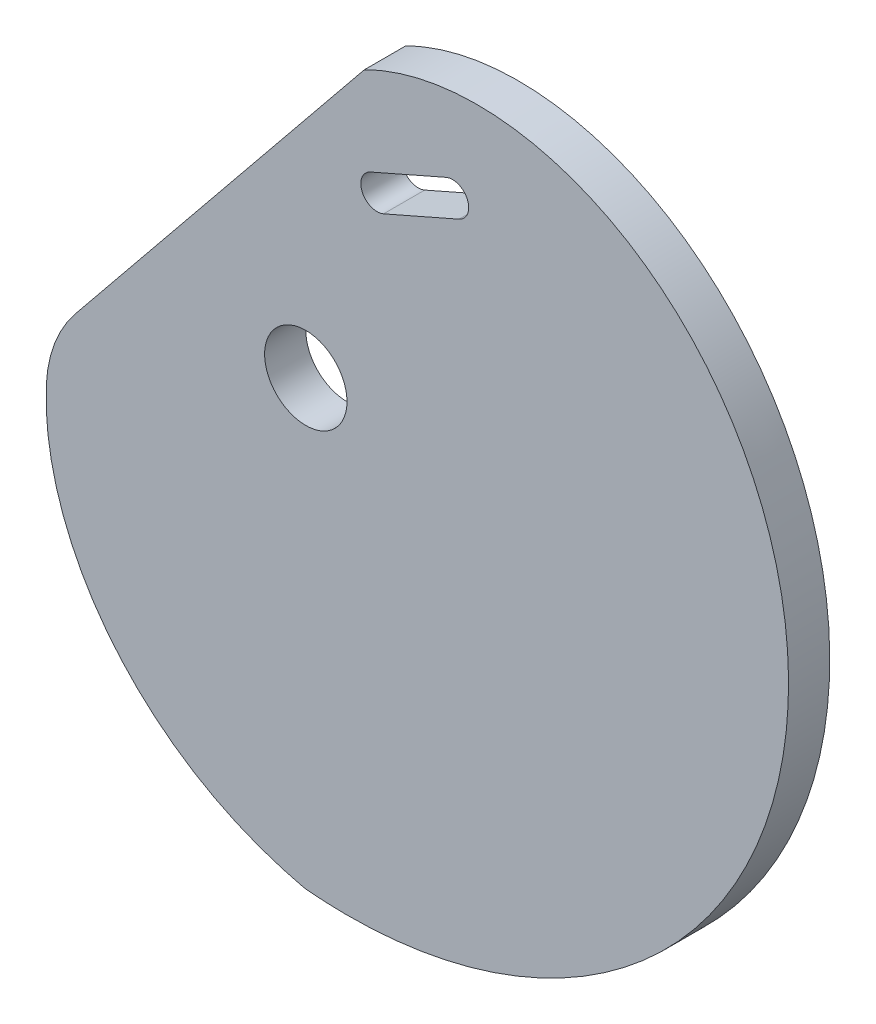
SolidWorks part; units mm, degrees
ref_plane "Front Plane" through (0, 0, 0) normal (0, 0, 1) x (1, 0, 0)
ref_plane "Top Plane" through (0, 0, 0) normal (0, 1, 0) x (1, 0, 0)
ref_plane "Right Plane" through (0, 0, 0) normal (1, 0, 0) x (0, 0, -1)
curve "Curve1"
sketch "Sketch1" plane through (0, 0, 0) normal (0, 0, 1) x (1, 0, 0)
  line L0 (10.9805, 30.1851) -> (22.6104, 35.2876) construction
  line L1 (9.976, 32.4744) -> (21.6059, 37.5769)
  line L2 (11.9849, 27.8957) -> (23.6148, 32.9983)
  line L3 (10.7688, 46.4724) -> (16.7954, 32.7363) construction
  line L4 (-15.5247, -36.542) -> (-17.0714, -47.8252) construction
  line L5 (-12.072, -37.0153) -> (-13.6188, -48.2986) construction
  line L6 (-18.9773, -36.0687) -> (-20.5241, -47.3519) construction
  line L7 (-15.1851, -34.0651) -> (-15.8642, -39.0188) construction
  circle A0 centre (0, 0) radius 6.35
  arc A1 (9.976, 32.4744) -> (11.9849, 27.8957) centre (10.9805, 30.1851) ccw
  arc A2 (23.6148, 32.9983) -> (21.6059, 37.5769) centre (22.6104, 35.2876) ccw
  arc A4 (-12.072, -37.0153) -> (-18.9773, -36.0687) centre (-15.5247, -36.542) ccw construction
  arc A5 (-20.5241, -47.3519) -> (-13.6188, -48.2986) centre (-17.0714, -47.8252) ccw construction
  spline S1 degree 3 poles (-1.1843, -67.9504) (-0.014, -68.2767) (1.195, -68.3213) (2.3889, -68.4148) (3.5889, -68.4701) (4.791, -68.5105) (5.9959, -68.5295) (7.203, -68.5287) (8.412, -68.5074) (9.6226, -68.4657) (10.8344, -68.4032) (12.047, -68.32) (13.2602, -68.2159) (14.4735, -68.0908) (15.6866, -67.9446) (16.8991, -67.777) (18.1106, -67.5882) (19.3207, -67.3779) (20.529, -67.1461) (21.7351, -66.8927) (22.9386, -66.6176) (24.1392, -66.3208) (25.3362, -66.0022) (26.5295, -65.6619) (27.7184, -65.2996) (28.9026, -64.9155) (30.0816, -64.5096) (31.2551, -64.0817) (32.4225, -63.632) (33.5833, -63.1604) (34.7372, -62.667) (35.8837, -62.1518) (37.0223, -61.6149) (38.1525, -61.0563) (39.2739, -60.4761) (40.3861, -59.8743) (41.4885, -59.2512) (42.5806, -58.6068) (43.6621, -57.9411) (44.7324, -57.2544) (45.791, -56.5468) (46.8375, -55.8184) (47.8714, -55.0695) (48.8923, -54.3001) (49.8996, -53.5105) (50.8929, -52.7009) (51.8717, -51.8715) (52.8356, -51.0225) (53.7841, -50.1542) (54.7166, -49.2668) (55.6329, -48.3607) (56.5323, -47.436) (57.4145, -46.4932) (58.279, -45.5324) (59.1254, -44.554) (59.9531, -43.5583) (60.7619, -42.5458) (61.5512, -41.5167) (62.3207, -40.4714) (63.0698, -39.4103) (63.7983, -38.3338) (64.5057, -37.2423) (65.1916, -36.1362) (65.8556, -35.016) (66.4973, -33.882) (67.1165, -32.7348) (67.7126, -31.5748) (68.2854, -30.4026) (68.8345, -29.2185) (69.3596, -28.023) (69.8603, -26.8168) (70.3364, -25.6003) (70.7876, -24.3741) (71.2134, -23.1386) (71.6138, -21.8945) (71.9884, -20.6423) (72.337, -19.3826) (72.6592, -18.116) (72.955, -16.843) (73.224, -15.5643) (73.4661, -14.2804) (73.6812, -12.992) (73.8689, -11.6997) (74.0292, -10.4042) (74.1619, -9.106) (74.2669, -7.8058) (74.3441, -6.5043) (74.3933, -5.2021) (74.4146, -3.9) (74.4078, -2.5984) (74.3729, -1.2982) (74.3098, -0.0001) (74.2186, 1.2954) (74.0993, 2.5875) (73.9518, 3.8756) (73.7762, 5.1589) (73.5725, 6.4367) (73.3409, 7.7084) (73.0814, 8.9732) (72.7942, 10.2305) (72.4792, 11.4795) (72.1368, 12.7196) (71.767, 13.95) (71.3701, 15.1701) (70.9462, 16.3792) (70.4955, 17.5765) (70.0184, 18.7613) (69.515, 19.9331) (68.9856, 21.091) (68.4305, 22.2344) (67.85, 23.3626) (67.2445, 24.475) (66.6143, 25.5709) (65.9598, 26.6495) (65.2813, 27.7103) (64.5793, 28.7526) (63.8542, 29.7758) (63.1064, 30.7792) (62.3364, 31.7621) (61.5447, 32.7241) (60.7318, 33.6643) (59.8981, 34.5824) (59.0442, 35.4776) (58.1707, 36.3494) (57.2782, 37.1972) (56.3671, 38.0204) (55.4383, 38.8186) (54.4923, 39.5913) (53.53, 40.3381) (52.552, 41.0585) (51.5591, 41.7521) (50.552, 42.4186) (49.5315, 43.0576) (48.4984, 43.6687) (47.4535, 44.2516) (46.3974, 44.8061) (45.3311, 45.3318) (44.2553, 45.8284) (43.1709, 46.2958) (42.0786, 46.7338) (40.9793, 47.1421) (39.8737, 47.5205) (38.7628, 47.869) (37.6473, 48.1874) (36.5281, 48.4755) (35.4061, 48.7334) (34.282, 48.961) (33.1567, 49.1581) (32.031, 49.3249) (30.9059, 49.4613) (29.7821, 49.5673) (28.6604, 49.6431) (27.5418, 49.6886) (26.427, 49.7041) (25.3169, 49.6895) (24.2124, 49.6451) (23.1141, 49.571) (22.0231, 49.4674) (20.94, 49.3346) (19.8657, 49.1727) (18.801, 48.982) (17.7468, 48.7628) (16.7037, 48.5154) (15.6726, 48.2401) (14.6543, 47.9373) (13.6495, 47.6073) (12.659, 47.2504) (11.6836, 46.8672) (10.7239, 46.458) (9.7807, 46.0233) (8.8547, 45.5635) (7.9467, 45.0791) (7.0573, 44.5706) (6.1871, 44.0386) (5.3369, 43.4835) (4.5074, 42.906) (3.699, 42.3065) (2.9126, 41.6858) (2.1491, 41.0448) (1.4087, 40.3857) (0.692, 39.711) (-0.0007, 39.0233) (-0.6692, 38.3252) (-1.3135, 37.6192) (-1.9336, 36.908) (-2.5298, 36.194) (-3.1024, 35.4799) (-3.6521, 34.7682) (-4.1795, 34.0612) (-4.6854, 33.3616) (-5.1709, 32.6716) (-5.637, 31.9937) (-6.085, 31.3301) (-6.5163, 30.6831) (-6.9325, 30.0548) (-7.3352, 29.4474) (-7.7263, 28.8629) (-8.1078, 28.3032) (-8.4816, 27.77) (-8.8501, 27.2652) (-9.216, 26.7897) (-9.5801, 26.3424) (-9.9432, 25.9213) (-10.3062, 25.5243) (-10.6698, 25.1494) (-11.0346, 24.7946) (-11.4009, 24.4578) (-11.7691, 24.1369) (-12.1394, 23.8299) (-12.5117, 23.5348) (-12.8861, 23.2497) (-13.2622, 22.9725) (-13.6397, 22.7014) (-14.0182, 22.4345) (-14.3971, 22.1699) (-14.7757, 21.906) (-15.1531, 21.6409) (-15.5285, 21.3732) (-15.9009, 21.1012) (-16.269, 20.8234) (-16.6317, 20.5384) (-16.9875, 20.2449) (-17.3351, 19.9417) (-17.6745, 19.6295) (-18.0059, 19.3089) (-18.3295, 18.9807) (-18.6455, 18.6455) (-18.9542, 18.3039) (-19.2559, 17.9565) (-19.5509, 17.6038) (-19.8396, 17.2464) (-20.1224, 16.8848) (-20.3997, 16.5195) (-20.672, 16.1508) (-20.9397, 15.7793) (-21.2033, 15.4052) (-21.4634, 15.0289) (-21.7205, 14.6507) (-21.9753, 14.2708) (-22.2281, 13.8895) (-22.4798, 13.507) (-22.7308, 13.1233) (-22.9819, 12.7386) (-23.2336, 12.3529) (-23.4866, 11.9663) (-23.7416, 11.5787) (-23.9993, 11.19) (-24.2602, 10.8001) (-24.5251, 10.4088) (-24.7947, 10.016) (-25.0696, 9.6214) (-25.3504, 9.2246) (-25.6379, 8.8254) (-25.9327, 8.4234) (-26.2354, 8.018) (-26.5467, 7.609) (-26.8672, 7.1956) (-27.1974, 6.7776) (-27.537, 6.3539) (-27.8856, 5.9238) (-28.2424, 5.4864) (-28.6069, 5.0408) (-28.9783, 4.5865) (-29.3562, 4.1226) (-29.7396, 3.6485) (-30.1278, 3.1637) (-30.5202, 2.6674) (-30.9158, 2.1592) (-31.314, 1.6386) (-31.7137, 1.1051) (-32.1143, 0.5583) (-32.5148, -0.0021) (-32.9143, -0.5765) (-33.3119, -1.1651) (-33.7067, -1.7682) (-34.0978, -2.3859) (-34.4843, -3.0184) (-34.8652, -3.6658) (-35.2396, -4.3281) (-35.6066, -5.0053) (-35.9651, -5.6973) (-36.3143, -6.404) (-36.6531, -7.1254) (-36.9808, -7.8611) (-37.2963, -8.611) (-37.5988, -9.3748) (-37.8873, -10.1521) (-38.1609, -10.9426) (-38.4187, -11.7459) (-38.66, -12.5613) (-38.8837, -13.3886) (-39.0892, -14.2271) (-39.2755, -15.0762) (-39.4422, -15.9354) (-39.589, -16.8043) (-39.7155, -17.6823) (-39.8215, -18.5689) (-39.9067, -19.4636) (-39.9709, -20.366) (-40.0137, -21.2755) (-40.035, -22.1916) (-40.0345, -23.1138) (-40.0119, -24.0415) (-39.9672, -24.9742) (-39.9002, -25.9114) (-39.8105, -26.8525) (-39.6982, -27.7969) (-39.563, -28.7442) (-39.4048, -29.6936) (-39.2235, -30.6448) (-39.019, -31.597) (-38.7911, -32.5497) (-38.5399, -33.5023) (-38.2653, -34.4543) (-37.9672, -35.4051) (-37.6456, -36.354) (-37.3004, -37.3005) (-36.9317, -38.2441) (-36.5395, -39.184) (-36.1238, -40.1197) (-35.6847, -41.0507) (-35.2221, -41.9763) (-34.7363, -42.896) (-34.2272, -43.8091) (-33.695, -44.715) (-33.1398, -45.6133) (-32.5617, -46.5032) (-31.9609, -47.3843) (-31.3375, -48.2559) (-30.6917, -49.1174) (-30.0238, -49.9683) (-29.3338, -50.808) (-28.6221, -51.636) (-27.8888, -52.4517) (-27.1343, -53.2545) (-26.3587, -54.0439) (-25.5624, -54.8193) (-24.7457, -55.5802) (-23.9088, -56.3261) (-23.0521, -57.0564) (-22.1759, -57.7707) (-21.2805, -58.4684) (-20.3664, -59.149) (-19.4339, -59.812) (-18.4833, -60.4569) (-17.5151, -61.0833) (-16.5298, -61.6908) (-15.5276, -62.2787) (-14.5091, -62.8467) (-13.4747, -63.3944) (-12.4248, -63.9213) (-11.36, -64.4271) (-10.2807, -64.9112) (-9.1874, -65.3733) (-8.0806, -65.8131) (-6.9608, -66.2301) (-5.8286, -66.6239) (-4.6845, -66.9947) (-3.5289, -67.3403) (-2.3631, -67.6669) (-1.1843, -67.9504) (-0.014, -68.2767) (1.195, -68.3213) knots -0.0101 -0.006743 -0.003377 0 0.00332 0.006645 0.009976 0.013312 0.016655 0.020003 0.023357 0.026716 0.030082 0.033453 0.036831 0.040214 0.043603 0.046998 0.050399 0.053806 0.057218 0.060637 0.064061 0.067491 0.070927 0.074369 0.077816 0.081269 0.084728 0.088192 0.091662 0.095138 0.098619 0.102105 0.105597 0.109094 0.112596 0.116103 0.119615 0.123133 0.126655 0.130182 0.133714 0.137251 0.140792 0.144337 0.147888 0.151442 0.155 0.158563 0.16213 0.1657 0.169275 0.172853 0.176434 0.180019 0.183607 0.187199 0.190793 0.19439 0.19799 0.201593 0.205199 0.208806 0.212416 0.216028 0.219642 0.223258 0.226875 0.230494 0.234115 0.237736 0.241359 0.244982 0.248606 0.252231 0.255856 0.259481 0.263106 0.266731 0.270356 0.273981 0.277605 0.281228 0.28485 0.28847 0.29209 0.295708 0.299324 0.302939 0.306551 0.310161 0.313769 0.317374 0.320976 0.324575 0.328171 0.331763 0.335352 0.338938 0.342519 0.346096 0.349669 0.353237 0.356801 0.360359 0.363913 0.367461 0.371004 0.374541 0.378073 0.381598 0.385117 0.38863 0.392136 0.395636 0.399128 0.402614 0.406092 0.409563 0.413026 0.416482 0.419929 0.423369 0.4268 0.430223 0.433637 0.437043 0.44044 0.443828 0.447206 0.450575 0.453935 0.457284 0.460624 0.463953 0.467272 0.47058 0.473877 0.477164 0.480439 0.483703 0.486955 0.490196 0.493426 0.496643 0.499848 0.503042 0.506223 0.509391 0.512547 0.515691 0.518822 0.52194 0.525045 0.528137 0.531216 0.534282 0.537335 0.540375 0.543401 0.546414 0.549414 0.5524 0.555374 0.558333 0.56128 0.564213 0.567133 0.57004 0.572933 0.575814 0.578681 0.581535 0.584377 0.587205 0.590021 0.592825 0.595616 0.598394 0.60116 0.603911 0.606642 0.60935 0.612032 0.614684 0.617303 0.619884 0.622424 0.62492 0.627367 0.629763 0.632104 0.634387 0.636609 0.638767 0.640858 0.64288 0.644831 0.64671 0.648517 0.65025 0.651911 0.653509 0.655048 0.656538 0.657984 0.659394 0.660772 0.662125 0.663458 0.664774 0.666078 0.667373 0.668662 0.669946 0.671227 0.672507 0.673786 0.675065 0.676344 0.677623 0.678903 0.680182 0.681461 0.68274 0.684019 0.685298 0.686575 0.687853 0.689129 0.690404 0.691679 0.692952 0.694224 0.695495 0.696765 0.698035 0.699304 0.700572 0.70184 0.703109 0.704379 0.705651 0.706925 0.708202 0.709483 0.71077 0.712063 0.713364 0.714674 0.715995 0.717328 0.718676 0.72004 0.721422 0.722825 0.72425 0.7257 0.727177 0.728683 0.730218 0.731784 0.73338 0.735008 0.736668 0.738359 0.740082 0.741837 0.743623 0.745441 0.747291 0.749171 0.751082 0.753022 0.754993 0.756992 0.759021 0.761077 0.76316 0.765271 0.767407 0.769569 0.771756 0.773967 0.776201 0.778458 0.780736 0.783036 0.785357 0.787697 0.790056 0.792433 0.794828 0.797239 0.799666 0.80211 0.804571 0.807047 0.80954 0.812049 0.814575 0.817116 0.819674 0.822248 0.824838 0.827444 0.830066 0.832704 0.835358 0.838027 0.840713 0.843414 0.846131 0.848864 0.851612 0.854376 0.857155 0.859949 0.862759 0.865584 0.868424 0.871279 0.874149 0.877033 0.879933 0.882847 0.885776 0.88872 0.891678 0.89465 0.897636 0.900637 0.903651 0.906679 0.909721 0.912777 0.915847 0.91893 0.922026 0.925135 0.928258 0.931393 0.934541 0.937702 0.940876 0.944062 0.947261 0.950471 0.953694 0.956929 0.960175 0.963433 0.966703 0.969984 0.973276 0.976579 0.979893 0.983218 0.986554 0.9899 0.993257 0.996623 1 1.00332 1.006645 1.009976 only from (0, -68.2309) to (0, -68.2309)
  point P6 (16.7954, 32.7363)
  point P18 (-16.298, -42.1836)
  dimension "D1" = 12.7
  dimension "D2" = 12.7
  dimension "D3" = 5
  dimension "D4" = 15
extrude "Boss-Extrude1" add sketch "Sketch1" along normal mid plane 6.35
sketch "Sketch2" plane through (0, 0, 0) normal (0, 0, 1) x (1, 0, 0)
  line L0 (7.479, 46.6391) -> (-35.7001, -3.6508) construction
  line L1 (-35.7001, -3.6508) -> (-5.287, 46.6391)
  line L2 (-5.287, 46.6391) -> (7.479, 46.6391)
  line L3 (9.0178, 45.6413) -> (-41.2002, -16.1969)
  line L4 (7.479, 46.6391) -> (9.0178, 45.6413)
  line L5 (-35.7001, -3.6508) -> (-41.2002, -16.1969)
  spline S0 degree 3 poles (-1.1843, -67.9504) (-0.014, -68.2767) (1.195, -68.3213) (2.3889, -68.4148) (3.5889, -68.4701) (4.791, -68.5105) (5.9959, -68.5295) (7.203, -68.5287) (8.412, -68.5074) (9.6226, -68.4657) (10.8344, -68.4032) (12.047, -68.32) (13.2602, -68.2159) (14.4735, -68.0908) (15.6866, -67.9446) (16.8991, -67.777) (18.1106, -67.5882) (19.3207, -67.3779) (20.529, -67.1461) (21.7351, -66.8927) (22.9386, -66.6176) (24.1392, -66.3208) (25.3362, -66.0022) (26.5295, -65.6619) (27.7184, -65.2996) (28.9026, -64.9155) (30.0816, -64.5096) (31.2551, -64.0817) (32.4225, -63.632) (33.5833, -63.1604) (34.7372, -62.667) (35.8837, -62.1518) (37.0223, -61.6149) (38.1525, -61.0563) (39.2739, -60.4761) (40.3861, -59.8743) (41.4885, -59.2512) (42.5806, -58.6068) (43.6621, -57.9411) (44.7324, -57.2544) (45.791, -56.5468) (46.8375, -55.8184) (47.8714, -55.0695) (48.8923, -54.3001) (49.8996, -53.5105) (50.8929, -52.7009) (51.8717, -51.8715) (52.8356, -51.0225) (53.7841, -50.1542) (54.7166, -49.2668) (55.6329, -48.3607) (56.5323, -47.436) (57.4145, -46.4932) (58.279, -45.5324) (59.1254, -44.554) (59.9531, -43.5583) (60.7619, -42.5458) (61.5512, -41.5167) (62.3207, -40.4714) (63.0698, -39.4103) (63.7983, -38.3338) (64.5057, -37.2423) (65.1916, -36.1362) (65.8556, -35.016) (66.4973, -33.882) (67.1165, -32.7348) (67.7126, -31.5748) (68.2854, -30.4026) (68.8345, -29.2185) (69.3596, -28.023) (69.8603, -26.8168) (70.3364, -25.6003) (70.7876, -24.3741) (71.2134, -23.1386) (71.6138, -21.8945) (71.9884, -20.6423) (72.337, -19.3826) (72.6592, -18.116) (72.955, -16.843) (73.224, -15.5643) (73.4661, -14.2804) (73.6812, -12.992) (73.8689, -11.6997) (74.0292, -10.4042) (74.1619, -9.106) (74.2669, -7.8058) (74.3441, -6.5043) (74.3933, -5.2021) (74.4146, -3.9) (74.4078, -2.5984) (74.3729, -1.2982) (74.3098, -0.0001) (74.2186, 1.2954) (74.0993, 2.5875) (73.9518, 3.8756) (73.7762, 5.1589) (73.5725, 6.4367) (73.3409, 7.7084) (73.0814, 8.9732) (72.7942, 10.2305) (72.4792, 11.4795) (72.1368, 12.7196) (71.767, 13.95) (71.3701, 15.1701) (70.9462, 16.3792) (70.4955, 17.5765) (70.0184, 18.7613) (69.515, 19.9331) (68.9856, 21.091) (68.4305, 22.2344) (67.85, 23.3626) (67.2445, 24.475) (66.6143, 25.5709) (65.9598, 26.6495) (65.2813, 27.7103) (64.5793, 28.7526) (63.8542, 29.7758) (63.1064, 30.7792) (62.3364, 31.7621) (61.5447, 32.7241) (60.7318, 33.6643) (59.8981, 34.5824) (59.0442, 35.4776) (58.1707, 36.3494) (57.2782, 37.1972) (56.3671, 38.0204) (55.4383, 38.8186) (54.4923, 39.5913) (53.53, 40.3381) (52.552, 41.0585) (51.5591, 41.7521) (50.552, 42.4186) (49.5315, 43.0576) (48.4984, 43.6687) (47.4535, 44.2516) (46.3974, 44.8061) (45.3311, 45.3318) (44.2553, 45.8284) (43.1709, 46.2958) (42.0786, 46.7338) (40.9793, 47.1421) (39.8737, 47.5205) (38.7628, 47.869) (37.6473, 48.1874) (36.5281, 48.4755) (35.4061, 48.7334) (34.282, 48.961) (33.1567, 49.1581) (32.031, 49.3249) (30.9059, 49.4613) (29.7821, 49.5673) (28.6604, 49.6431) (27.5418, 49.6886) (26.427, 49.7041) (25.3169, 49.6895) (24.2124, 49.6451) (23.1141, 49.571) (22.0231, 49.4674) (20.94, 49.3346) (19.8657, 49.1727) (18.801, 48.982) (17.7468, 48.7628) (16.7037, 48.5154) (15.6726, 48.2401) (14.6543, 47.9373) (13.6495, 47.6073) (12.659, 47.2504) (11.6836, 46.8672) (10.7239, 46.458) (9.7807, 46.0233) (8.8547, 45.5635) (7.9467, 45.0791) (7.0573, 44.5706) (6.1871, 44.0386) (5.3369, 43.4835) (4.5074, 42.906) (3.699, 42.3065) (2.9126, 41.6858) (2.1491, 41.0448) (1.4087, 40.3857) (0.692, 39.711) (-0.0007, 39.0233) (-0.6692, 38.3252) (-1.3135, 37.6192) (-1.9336, 36.908) (-2.5298, 36.194) (-3.1024, 35.4799) (-3.6521, 34.7682) (-4.1795, 34.0612) (-4.6854, 33.3616) (-5.1709, 32.6716) (-5.637, 31.9937) (-6.085, 31.3301) (-6.5163, 30.6831) (-6.9325, 30.0548) (-7.3352, 29.4474) (-7.7263, 28.8629) (-8.1078, 28.3032) (-8.4816, 27.77) (-8.8501, 27.2652) (-9.216, 26.7897) (-9.5801, 26.3424) (-9.9432, 25.9213) (-10.3062, 25.5243) (-10.6698, 25.1494) (-11.0346, 24.7946) (-11.4009, 24.4578) (-11.7691, 24.1369) (-12.1394, 23.8299) (-12.5117, 23.5348) (-12.8861, 23.2497) (-13.2622, 22.9725) (-13.6397, 22.7014) (-14.0182, 22.4345) (-14.3971, 22.1699) (-14.7757, 21.906) (-15.1531, 21.6409) (-15.5285, 21.3732) (-15.9009, 21.1012) (-16.269, 20.8234) (-16.6317, 20.5384) (-16.9875, 20.2449) (-17.3351, 19.9417) (-17.6745, 19.6295) (-18.0059, 19.3089) (-18.3295, 18.9807) (-18.6455, 18.6455) (-18.9542, 18.3039) (-19.2559, 17.9565) (-19.5509, 17.6038) (-19.8396, 17.2464) (-20.1224, 16.8848) (-20.3997, 16.5195) (-20.672, 16.1508) (-20.9397, 15.7793) (-21.2033, 15.4052) (-21.4634, 15.0289) (-21.7205, 14.6507) (-21.9753, 14.2708) (-22.2281, 13.8895) (-22.4798, 13.507) (-22.7308, 13.1233) (-22.9819, 12.7386) (-23.2336, 12.3529) (-23.4866, 11.9663) (-23.7416, 11.5787) (-23.9993, 11.19) (-24.2602, 10.8001) (-24.5251, 10.4088) (-24.7947, 10.016) (-25.0696, 9.6214) (-25.3504, 9.2246) (-25.6379, 8.8254) (-25.9327, 8.4234) (-26.2354, 8.018) (-26.5467, 7.609) (-26.8672, 7.1956) (-27.1974, 6.7776) (-27.537, 6.3539) (-27.8856, 5.9238) (-28.2424, 5.4864) (-28.6069, 5.0408) (-28.9783, 4.5865) (-29.3562, 4.1226) (-29.7396, 3.6485) (-30.1278, 3.1637) (-30.5202, 2.6674) (-30.9158, 2.1592) (-31.314, 1.6386) (-31.7137, 1.1051) (-32.1143, 0.5583) (-32.5148, -0.0021) (-32.9143, -0.5765) (-33.3119, -1.1651) (-33.7067, -1.7682) (-34.0978, -2.3859) (-34.4843, -3.0184) (-34.8652, -3.6658) (-35.2396, -4.3281) (-35.6066, -5.0053) (-35.9651, -5.6973) (-36.3143, -6.404) (-36.6531, -7.1254) (-36.9808, -7.8611) (-37.2963, -8.611) (-37.5988, -9.3748) (-37.8873, -10.1521) (-38.1609, -10.9426) (-38.4187, -11.7459) (-38.66, -12.5613) (-38.8837, -13.3886) (-39.0892, -14.2271) (-39.2755, -15.0762) (-39.4422, -15.9354) (-39.589, -16.8043) (-39.7155, -17.6823) (-39.8215, -18.5689) (-39.9067, -19.4636) (-39.9709, -20.366) (-40.0137, -21.2755) (-40.035, -22.1916) (-40.0345, -23.1138) (-40.0119, -24.0415) (-39.9672, -24.9742) (-39.9002, -25.9114) (-39.8105, -26.8525) (-39.6982, -27.7969) (-39.563, -28.7442) (-39.4048, -29.6936) (-39.2235, -30.6448) (-39.019, -31.597) (-38.7911, -32.5497) (-38.5399, -33.5023) (-38.2653, -34.4543) (-37.9672, -35.4051) (-37.6456, -36.354) (-37.3004, -37.3005) (-36.9317, -38.2441) (-36.5395, -39.184) (-36.1238, -40.1197) (-35.6847, -41.0507) (-35.2221, -41.9763) (-34.7363, -42.896) (-34.2272, -43.8091) (-33.695, -44.715) (-33.1398, -45.6133) (-32.5617, -46.5032) (-31.9609, -47.3843) (-31.3375, -48.2559) (-30.6917, -49.1174) (-30.0238, -49.9683) (-29.3338, -50.808) (-28.6221, -51.636) (-27.8888, -52.4517) (-27.1343, -53.2545) (-26.3587, -54.0439) (-25.5624, -54.8193) (-24.7457, -55.5802) (-23.9088, -56.3261) (-23.0521, -57.0564) (-22.1759, -57.7707) (-21.2805, -58.4684) (-20.3664, -59.149) (-19.4339, -59.812) (-18.4833, -60.4569) (-17.5151, -61.0833) (-16.5298, -61.6908) (-15.5276, -62.2787) (-14.5091, -62.8467) (-13.4747, -63.3944) (-12.4248, -63.9213) (-11.36, -64.4271) (-10.2807, -64.9112) (-9.1874, -65.3733) (-8.0806, -65.8131) (-6.9608, -66.2301) (-5.8286, -66.6239) (-4.6845, -66.9947) (-3.5289, -67.3403) (-2.3631, -67.6669) (-1.1843, -67.9504) (-0.014, -68.2767) (1.195, -68.3213) knots -0.0101 -0.006743 -0.003377 0 0.00332 0.006645 0.009976 0.013312 0.016655 0.020003 0.023357 0.026716 0.030082 0.033453 0.036831 0.040214 0.043603 0.046998 0.050399 0.053806 0.057218 0.060637 0.064061 0.067491 0.070927 0.074369 0.077816 0.081269 0.084728 0.088192 0.091662 0.095138 0.098619 0.102105 0.105597 0.109094 0.112596 0.116103 0.119615 0.123133 0.126655 0.130182 0.133714 0.137251 0.140792 0.144337 0.147888 0.151442 0.155 0.158563 0.16213 0.1657 0.169275 0.172853 0.176434 0.180019 0.183607 0.187199 0.190793 0.19439 0.19799 0.201593 0.205199 0.208806 0.212416 0.216028 0.219642 0.223258 0.226875 0.230494 0.234115 0.237736 0.241359 0.244982 0.248606 0.252231 0.255856 0.259481 0.263106 0.266731 0.270356 0.273981 0.277605 0.281228 0.28485 0.28847 0.29209 0.295708 0.299324 0.302939 0.306551 0.310161 0.313769 0.317374 0.320976 0.324575 0.328171 0.331763 0.335352 0.338938 0.342519 0.346096 0.349669 0.353237 0.356801 0.360359 0.363913 0.367461 0.371004 0.374541 0.378073 0.381598 0.385117 0.38863 0.392136 0.395636 0.399128 0.402614 0.406092 0.409563 0.413026 0.416482 0.419929 0.423369 0.4268 0.430223 0.433637 0.437043 0.44044 0.443828 0.447206 0.450575 0.453935 0.457284 0.460624 0.463953 0.467272 0.47058 0.473877 0.477164 0.480439 0.483703 0.486955 0.490196 0.493426 0.496643 0.499848 0.503042 0.506223 0.509391 0.512547 0.515691 0.518822 0.52194 0.525045 0.528137 0.531216 0.534282 0.537335 0.540375 0.543401 0.546414 0.549414 0.5524 0.555374 0.558333 0.56128 0.564213 0.567133 0.57004 0.572933 0.575814 0.578681 0.581535 0.584377 0.587205 0.590021 0.592825 0.595616 0.598394 0.60116 0.603911 0.606642 0.60935 0.612032 0.614684 0.617303 0.619884 0.622424 0.62492 0.627367 0.629763 0.632104 0.634387 0.636609 0.638767 0.640858 0.64288 0.644831 0.64671 0.648517 0.65025 0.651911 0.653509 0.655048 0.656538 0.657984 0.659394 0.660772 0.662125 0.663458 0.664774 0.666078 0.667373 0.668662 0.669946 0.671227 0.672507 0.673786 0.675065 0.676344 0.677623 0.678903 0.680182 0.681461 0.68274 0.684019 0.685298 0.686575 0.687853 0.689129 0.690404 0.691679 0.692952 0.694224 0.695495 0.696765 0.698035 0.699304 0.700572 0.70184 0.703109 0.704379 0.705651 0.706925 0.708202 0.709483 0.71077 0.712063 0.713364 0.714674 0.715995 0.717328 0.718676 0.72004 0.721422 0.722825 0.72425 0.7257 0.727177 0.728683 0.730218 0.731784 0.73338 0.735008 0.736668 0.738359 0.740082 0.741837 0.743623 0.745441 0.747291 0.749171 0.751082 0.753022 0.754993 0.756992 0.759021 0.761077 0.76316 0.765271 0.767407 0.769569 0.771756 0.773967 0.776201 0.778458 0.780736 0.783036 0.785357 0.787697 0.790056 0.792433 0.794828 0.797239 0.799666 0.80211 0.804571 0.807047 0.80954 0.812049 0.814575 0.817116 0.819674 0.822248 0.824838 0.827444 0.830066 0.832704 0.835358 0.838027 0.840713 0.843414 0.846131 0.848864 0.851612 0.854376 0.857155 0.859949 0.862759 0.865584 0.868424 0.871279 0.874149 0.877033 0.879933 0.882847 0.885776 0.88872 0.891678 0.89465 0.897636 0.900637 0.903651 0.906679 0.909721 0.912777 0.915847 0.91893 0.922026 0.925135 0.928258 0.931393 0.934541 0.937702 0.940876 0.944062 0.947261 0.950471 0.953694 0.956929 0.960175 0.963433 0.966703 0.969984 0.973276 0.976579 0.979893 0.983218 0.986554 0.9899 0.993257 0.996623 1 1.00332 1.006645 1.009976 only from (0, -68.2309) to (0, -68.2309) construction
extrude "Cut-Extrude1" cut sketch "Sketch2" against normal through all both and the other way through all
fillet "Fillet1" radius 20 1 edges at (-38.8618, -13.3174, 0)
sketch "Sketch3" plane through (0, 0, 3.175) normal (0, 0, 1) x (1, 0, 0)
  point P0 (-13.488, -5.936)
  point P1 (-3.3675, -25.0764)
  point P3 (-25.0038, -24.2708)
sketch "Sketch7" [suppressed] plane through (0, 0, 0) normal (0, 0, 1) x (1, 0, 0)
  circle A0 centre (0, 0) radius 6.35
  circle A1 centre (0, 0) radius 3.175
  dimension "D1" = 6.35
sketch "Sketch8" [suppressed] plane through (0, 0, 0) normal (0, 0, 1) x (1, 0, 0)
  line L0 (10.9805, 30.1851) -> (22.6104, 35.2876) construction
  line L1 (9.976, 32.4744) -> (21.6059, 37.5769)
  line L2 (11.9849, 27.8957) -> (23.6148, 32.9983)
  circle A0 centre (12.6554, 42.1677) radius 1
  arc A1 (5.6152, 38.2953) -> (20.342, 44.5764) centre (12.9786, 41.4359) ccw construction
  circle A2 centre (0, 0) radius 6.35
  arc A3 (9.976, 32.4744) -> (11.9849, 27.8957) centre (10.9805, 30.1851) ccw
  arc A4 (23.6148, 32.9983) -> (21.6059, 37.5769) centre (22.6104, 35.2876) ccw
  arc A5 (23.6148, 32.9983) -> (21.6059, 37.5769) centre (22.6104, 35.2876) ccw construction
  point P12 (16.7954, 32.7363)
  dimension "D2" = 2
  dimension "D1" = 0.8
sketch "Sketch15" plane through (0, 0, 3.175) normal (0, 0, 1) x (1, 0, 0)
  circle A0 centre (-43.3531, -41.4597) radius 1.1
  circle A1 centre (13.5262, -74.2009) radius 1.1
  dimension "D1" = 2.2
  dimension "D2" = 2.2
sketch "Sketch16" plane through (0, 0, 3.175) normal (0, 0, 1) x (1, 0, 0)
  circle A0 centre (-5.523, -52.2474) radius 1.05
  circle A1 centre (5.4449, -44.5935) radius 1.05
  circle A2 centre (10.1611, -19.1035) radius 1.1 construction
  circle A3 centre (-5.523, -52.2474) radius 1.05 construction
  circle A4 centre (5.4449, -44.5935) radius 1.05 construction
  circle A5 centre (10.1611, -19.1035) radius 1.1 construction
sketch "Sketch18" plane through (0, 0, 3.175) normal (0, 0, 1) x (1, 0, 0)
  circle A0 centre (-12.5246, -41.0492) radius 0.7
  circle A1 centre (0, -39.819) radius 0.7
  dimension "D1" = 1.4
  dimension "D2" = 1.4
